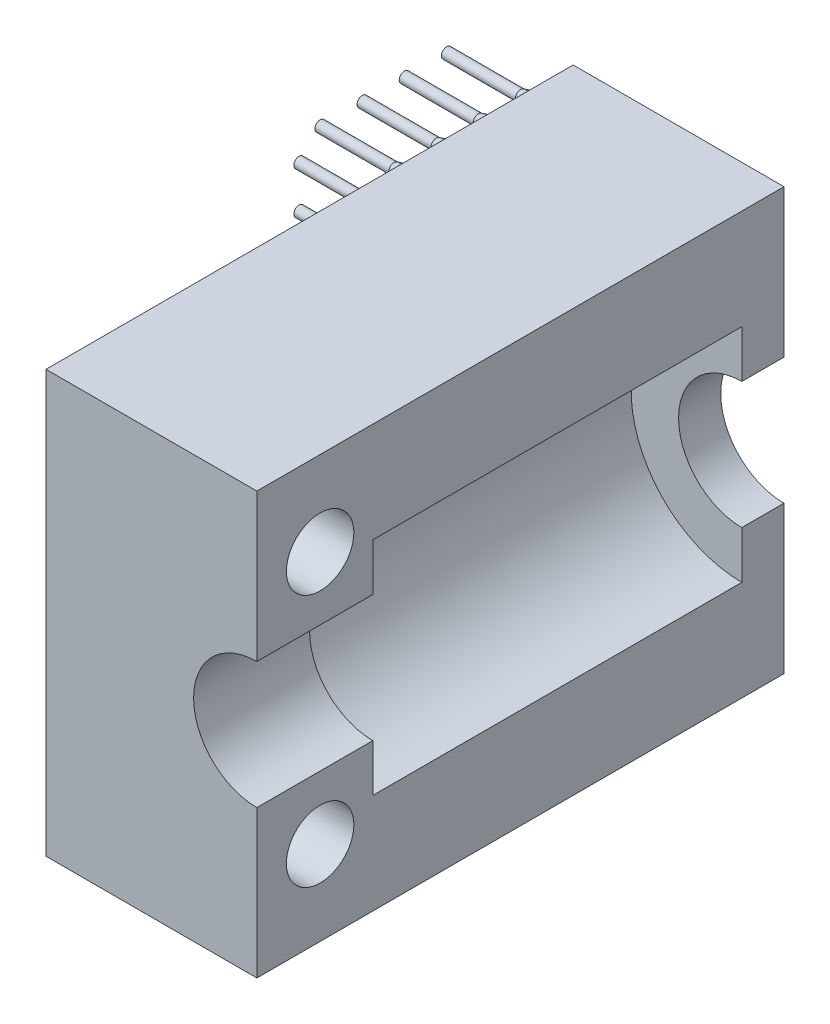
SolidWorks part; units mm, degrees
ref_plane "正面" through (0, 0, 0) normal (0, 0, 1) x (1, 0, 0)
ref_plane "平面" through (0, 0, 0) normal (0, 1, 0) x (1, 0, 0)
ref_plane "右側面" through (0, 0, 0) normal (1, 0, 0) x (0, 0, -1)
sketch "ｽｹｯﾁ1" plane through (0, 0, 0) normal (0, 0, 1) x (1, 0, 0)
  line L0 (0, 10) -> (-10, 10)
  line L1 (-10, 10) -> (-10, -10)
  line L2 (-10, -10) -> (0, -10)
  line L3 (0, 10) -> (0, 3)
  line L4 (0, -10) -> (0, -3)
  arc A0 (0, 3) -> (0, -3) centre (0, 0) ccw
  dimension "D1" = 6
extrude "ﾎﾞｽ - 押し出し1" add sketch "ｽｹｯﾁ1" along normal blind 25
sketch "ｽｹｯﾁ2" plane through (-10, 0, 0) normal (-1, 0, 0) x (0, 0, 1)
  line L0 (25, 10) -> (0, 10) construction
  line L1 (0, 10) -> (0, -10) construction
  circle A0 centre (1, 8.5) radius 0.25
  circle A1 centre (2, 7.5) radius 0.25
  dimension "D1" = 0.5
  dimension "D2" = 1.5
  dimension "D3" = 1
  dimension "D4" = 0.5
  dimension "D5" = 1
  dimension "D6" = 1
extrude "ﾎﾞｽ - 押し出し2" add sketch "ｽｹｯﾁ2" along normal blind 5
chamfer "面取り1" distance 0.4 angle 75 2 edges at (-10, 8.5, 0.75) (-10, 7.5, 1.75)
pattern_linear "直線ﾊﾟﾀｰﾝ1" count 4 spacing 2 along (0, 0, 1) count 9 spacing 2 along (0, -1, 0) of "ﾎﾞｽ - 押し出し2", "面取り1"
ref_plane "平面1" through (0, 0, 2) normal (0, 0, -1) x (-1, 0, 0)
sketch "ｽｹｯﾁ3" plane through (0, 0, 2) normal (0, 0, -1) x (-1, 0, 0)
  circle A0 centre (0, 0) radius 5.25
  dimension "D1" = 10.5
extrude "ｶｯﾄ - 押し出し1" cut sketch "ｽｹｯﾁ3" against normal blind 17.5
sketch "ｽｹｯﾁ4" plane through (0, 0, 0) normal (1, 0, 0) x (0, 0, -1)
  line L0 (0, 0) -> (-35.6149, 0) construction
  line L1 (-25, 10) -> (0, 10) construction
  line L2 (-25, 3) -> (-25, 10) construction
  circle A0 centre (-22, 6) radius 1.6
  circle A1 centre (-22, -6) radius 1.6
  dimension "D1" = 3.2
  dimension "D2" = 4
  dimension "D3" = 3
extrude "ｶｯﾄ - 押し出し2" cut sketch "ｽｹｯﾁ4" against normal through all
